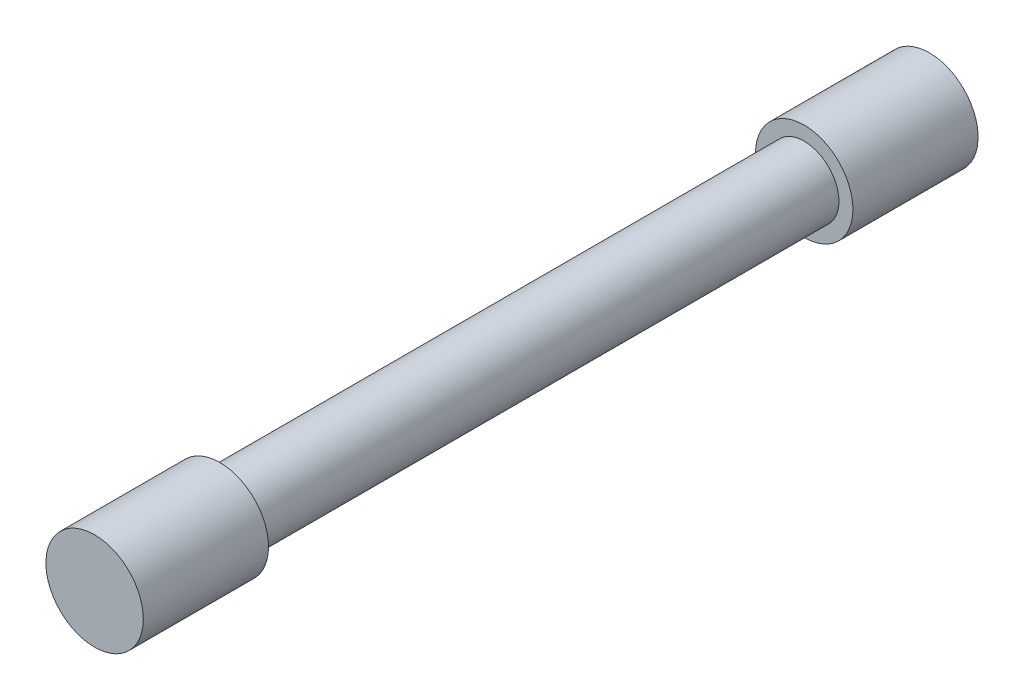
SolidWorks part; units mm, degrees
ref_plane "前视基准面" through (0, 0, 0) normal (0, 0, 1) x (1, 0, 0)
ref_plane "上视基准面" through (0, 0, 0) normal (0, 1, 0) x (1, 0, 0)
ref_plane "右视基准面" through (0, 0, 0) normal (1, 0, 0) x (0, 0, -1)
sketch "草图1" plane through (0, 0, 0) normal (0, 0, 1) x (1, 0, 0)
  circle A0 centre (0, 0) radius 7
  dimension "D1" = 14
extrude "凸台-拉伸1" add sketch "草图1" along normal blind 18
sketch "草图2" plane through (0, 0, 0) normal (0, 0, -1) x (-1, 0, 0)
  circle A0 centre (0, 0) radius 5
  dimension "D1" = 10
extrude "凸台-拉伸2" add sketch "草图2" along normal blind 84
sketch "草图3" plane through (0, 0, -84) normal (0, 0, -1) x (-1, 0, 0)
  circle A0 centre (0, 0) radius 7
  dimension "D1" = 14
extrude "凸台-拉伸3" add sketch "草图3" along normal blind 18
